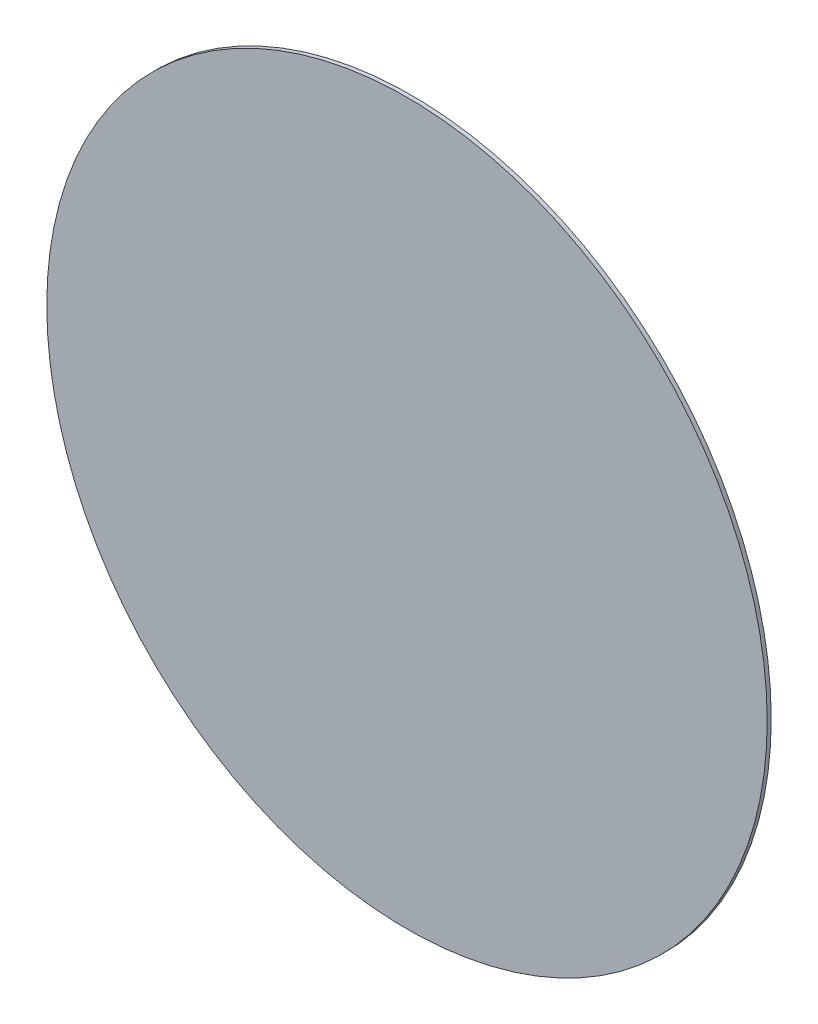
SolidWorks part; units mm, degrees
material "ABS PC"
ref_plane "Front Plane" through (0, 0, 0) normal (0, 0, 1) x (1, 0, 0)
ref_plane "Top Plane" through (0, 0, 0) normal (0, 1, 0) x (1, 0, 0)
ref_plane "Right Plane" through (0, 0, 0) normal (1, 0, 0) x (0, 0, -1)
sketch "Sketch1" plane through (0, 0, 0) normal (0, 0, 1) x (1, 0, 0)
  circle A0 centre (0, 0) radius 8.89
  dimension "D1" = 17.78
extrude "Boss-Extrude1" add sketch "Sketch1" along normal blind 0.0992
